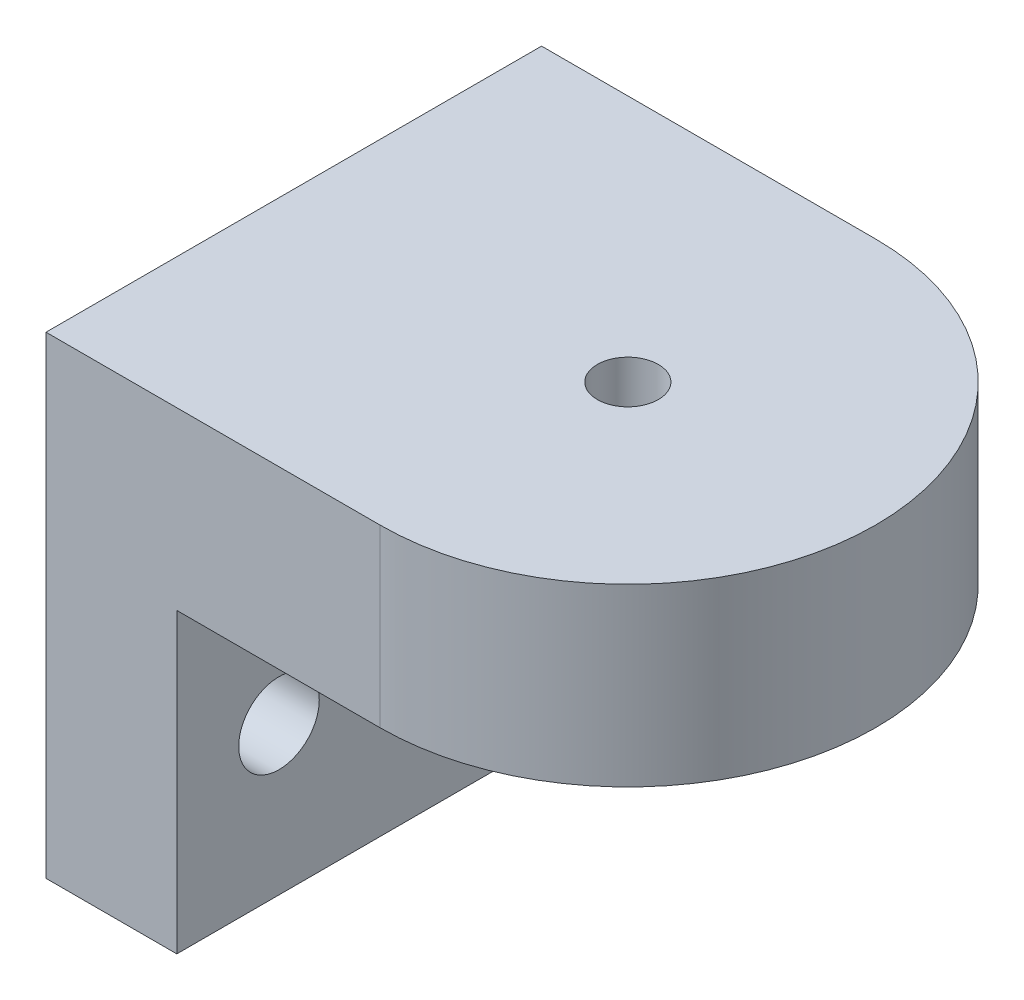
SolidWorks part; units mm, degrees
ref_plane "Front Plane" through (0, 0, 0) normal (0, 0, 1) x (1, 0, 0)
ref_plane "Top Plane" through (0, 0, 0) normal (0, 1, 0) x (1, 0, 0)
ref_plane "Right Plane" through (0, 0, 0) normal (1, 0, 0) x (0, 0, -1)
sketch "Sketch1" plane through (0, 0, 0) normal (1, 0, 0) x (0, 0, -1)
  line L1 (-17.0307, -16.256) -> (17.0307, -16.256)
  line L2 (-17.0307, -16.256) -> (-17.0307, 16.256)
  line L3 (-17.0307, 16.256) -> (17.0307, 16.256)
  line L4 (17.0307, -16.256) -> (17.0307, 16.256)
  line L5 (-17.0307, -16.256) -> (17.0307, 16.256) construction
  line L6 (-17.0307, 16.256) -> (17.0307, -16.256) construction
  point P0 (0, 0)
  dimension "D1" = 34.0614
  dimension "D2" = 32.512
extrude "Boss-Extrude1" add sketch "Sketch1" along normal blind 8.9916
sketch "Sketch2" plane through (8.9916, 0, 0) normal (1, 0, 0) x (0, 0, -1)
  line L0 (17.0307, -16.256) -> (17.0307, 16.256) construction
  line L1 (-17.0307, 16.256) -> (17.0307, 16.256)
  line L2 (-17.0307, 16.256) -> (-17.0307, 4.191)
  line L3 (-17.0307, 4.191) -> (17.0307, 4.191)
  line L4 (17.0307, 16.256) -> (17.0307, 4.191)
  dimension "D1" = 12.065
extrude "Boss-Extrude2" add sketch "Sketch2" along normal blind 13.97
sketch "Sketch3" plane through (22.9616, 0, 0) normal (1, 0, 0) x (0, 0, -1)
  line L0 (0, 16.256) -> (0, 4.191) construction
  line L1 (17.0307, 16.256) -> (-17.0307, 16.256) construction
  line L2 (-17.0307, 4.191) -> (17.0307, 4.191) construction
  line L4 (0, 16.256) -> (17.0307, 16.256)
  line L5 (0, 16.256) -> (0, 4.191)
  line L6 (0, 4.191) -> (17.0307, 4.191)
  line L7 (17.0307, 16.256) -> (17.0307, 4.191)
revolve "Revolve1" add sketch "Sketch3" angle 180 about L0
sketch "Sketch4" plane through (0, 16.256, 0) normal (0, 1, 0) x (1, 0, 0)
  line L2 (22.9616, 17.0307) -> (22.9616, -17.0307) construction
  arc A0 (22.9616, -17.0307) -> (22.9616, 17.0307) centre (22.9616, 0) ccw construction
  circle A1 centre (22.9616, 0) radius 2.0955
  dimension "D1" = 4.191
extrude "Cut-Extrude1" cut sketch "Sketch4" against normal blind 7.62
sketch "Sketch5" plane through (8.9916, 0, 0) normal (1, 0, 0) x (0, 0, -1)
  line L0 (-10.0076, -16.256) -> (-10.0076, 4.191) construction
  line L3 (-17.0307, -6.0325) -> (17.0307, -6.0325) construction
  line L4 (-17.0307, 4.191) -> (-17.0307, -16.256) construction
  line L5 (17.0307, -16.256) -> (17.0307, 4.191) construction
  line L6 (-17.0307, -16.256) -> (17.0307, -16.256) construction
  line L7 (-17.0307, 4.191) -> (17.0307, 4.191) construction
  line L8 (10.0076, -16.256) -> (10.0076, 4.191) construction
  circle A0 centre (-10.0076, -6.0325) radius 2.7686
  circle A1 centre (10.0076, -6.0325) radius 2.6416
  dimension "D3" = 5.5372
  dimension "D4" = 5.2832
  dimension "D1" = 7.0231
  dimension "D2" = 7.0231
extrude "Cut-Extrude2" cut sketch "Sketch5" against normal up to next
